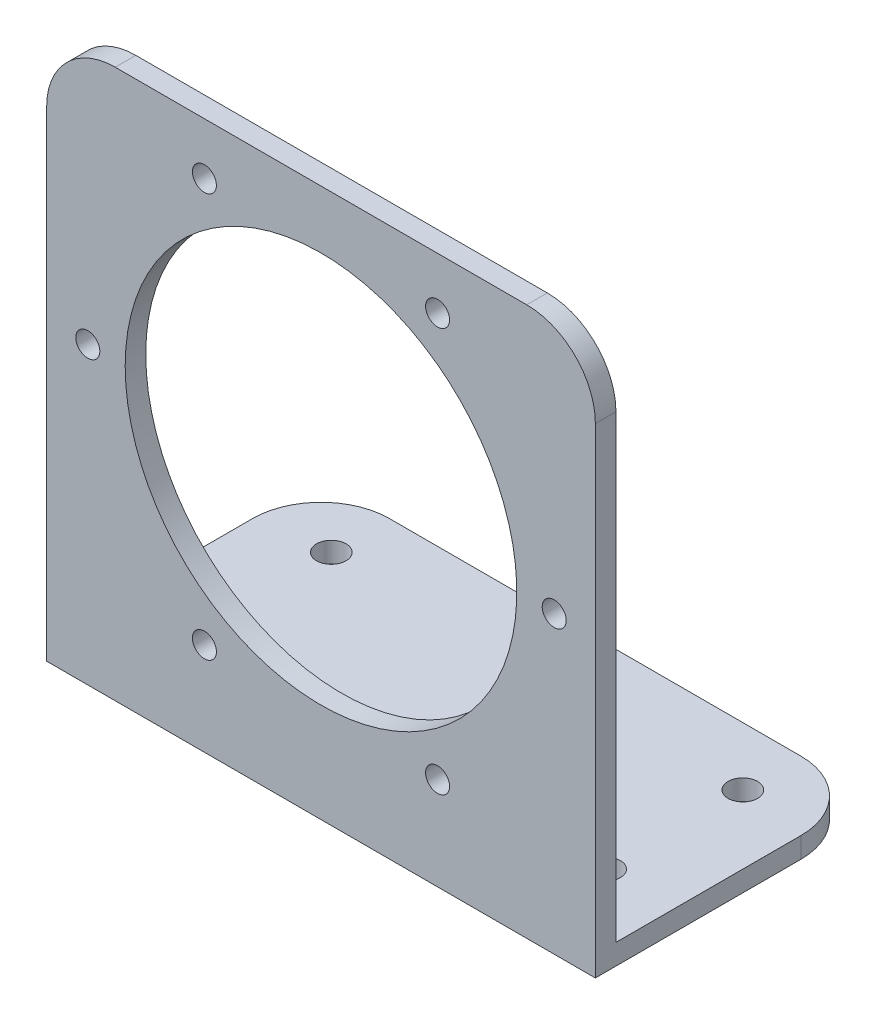
SolidWorks part; units mm, degrees
material "1060 合金"
ref_plane "前基準面" through (0, 0, 0) normal (0, 0, 1) x (1, 0, 0)
ref_plane "上基準面" through (0, 0, 0) normal (0, 1, 0) x (1, 0, 0)
ref_plane "右基準面" through (0, 0, 0) normal (1, 0, 0) x (0, 0, -1)
sketch "草圖2" plane through (0, 0, 0) normal (1, 0, 0) x (0, 0, -1)
  line L1 (0, 0) -> (3, 0)
  line L2 (0, 0) -> (0, 80)
  line L3 (0, 80) -> (3, 80)
  line L4 (3, 0) -> (3, 80)
  line L5 (3, 0) -> (40, 0)
  line L6 (3, 0) -> (3, 3)
  line L7 (3, 3) -> (40, 3)
  line L8 (40, 0) -> (40, 3)
  dimension "D1" = 80
  dimension "D2" = 40
  dimension "D3" = 3
  dimension "D4" = 3
extrude "填料-伸長1" add sketch "草圖2" along normal mid plane 80 contours L5 L8 L7 L4
sketch "草圖3" plane through (0, 0, -3) normal (0, 0, -1) x (-1, 0, 0)
  line L0 (0, 22) -> (0, -22) construction
  line L1 (0, 43) -> (17, 72.4449) construction
  line L2 (-40, 3) -> (40, 3) construction
  circle A0 centre (17, 72.4449) radius 1.75
  circle A1 centre (34, 43) radius 1.75
  circle A2 centre (17, 13.5551) radius 1.75
  circle A3 centre (-17, 13.5551) radius 1.75
  circle A4 centre (-34, 43) radius 1.75
  circle A5 centre (-17, 72.4449) radius 1.75
  circle A6 centre (0, 43) radius 28.55
  point P0 (0, 43)
  point P10 (0, 43)
  point P20 (0, 43)
  dimension "D3" = 3.5
  dimension "D6" = 57.1
  dimension "D1" = 30
  dimension "D2" = 34
  dimension "D4" = 40
  dimension "D5" = 6
extrude "motor_fixed_hole" cut sketch "草圖3" against normal through all
sketch "草圖4" plane through (0, 3, 0) normal (0, 1, 0) x (1, 0, 0)
  line L0 (-40, 21.5) -> (40, 21.5) construction
  line L1 (-40, 3) -> (-40, 40) construction
  line L2 (40, 3) -> (40, 40) construction
  line L3 (0, -22) -> (0, 22) construction
  circle A0 centre (-30, 31.5) radius 2.15
  circle A1 centre (-30, 11.5) radius 2.15
  circle A2 centre (30, 11.5) radius 2.15
  circle A3 centre (30, 31.5) radius 2.15
  dimension "D3" = 4.3
  dimension "D1" = 10
  dimension "D2" = 30
extrude "base_hole" cut sketch "草圖4" against normal through all
fillet "圓角1" radius 10 4 edges at (-40, 80, -1.5) (40, 80, -1.5) (-40, 1.5, -40) (40, 1.5, -40)
